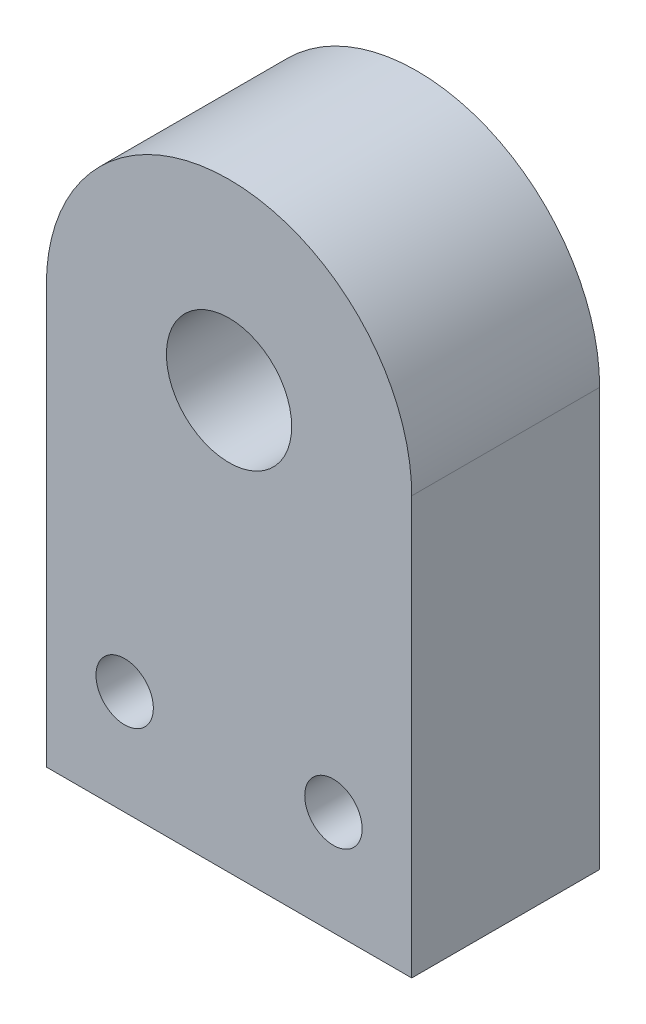
SolidWorks part; units mm, degrees
ref_plane "前视基准面" through (0, 0, 0) normal (0, 0, 1) x (1, 0, 0)
ref_plane "上视基准面" through (0, 0, 0) normal (0, 1, 0) x (1, 0, 0)
ref_plane "右视基准面" through (0, 0, 0) normal (1, 0, 0) x (0, 0, -1)
sketch "草图1" plane through (0, 0, 0) normal (0, 0, 1) x (1, 0, 0)
  line L0 (-17.5, 0) -> (-17.5, -40)
  line L1 (-17.5, -40) -> (17.5, -40)
  line L2 (17.5, 0) -> (17.5, -40)
  line L3 (0, 39.333) -> (0, -55.2174) construction
  line L4 (-32.5527, -30) -> (50.9493, -30) construction
  arc A0 (17.5, 0) -> (-17.5, 0) centre (0, 0) ccw
  circle A1 centre (0, 0) radius 6
  circle A2 centre (-10, -30) radius 2.75
  circle A3 centre (10, -30) radius 2.75
  dimension "D1" = 12
  dimension "D2" = 35
  dimension "D4" = 20
  dimension "D5" = 5.5
  dimension "D3" = 40
  dimension "D6" = 10
extrude "凸台-拉伸1" add sketch "草图1" along normal blind 18
